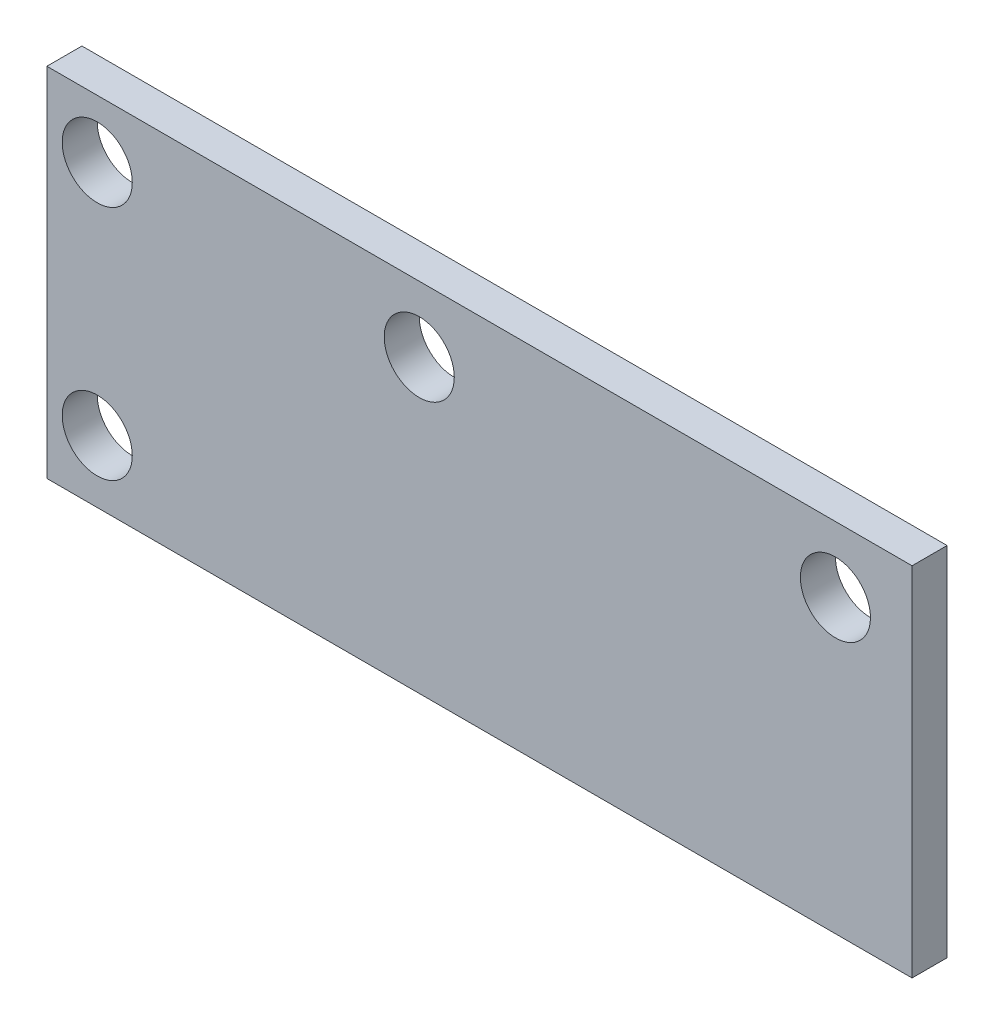
SolidWorks part; units mm, degrees
ref_plane "Piano frontale" through (0, 0, 0) normal (0, 0, 1) x (1, 0, 0)
ref_plane "Piano superiore" through (0, 0, 0) normal (0, 1, 0) x (1, 0, 0)
ref_plane "Piano destro" through (0, 0, 0) normal (1, 0, 0) x (0, 0, -1)
sketch "Schizzo1" plane through (0, 0, 0) normal (0, 0, 1) x (1, 0, 0)
  line L1 (-19.75, -8.15) -> (19.75, -8.15)
  line L2 (-19.75, -8.15) -> (-19.75, 8.15)
  line L3 (-19.75, 8.15) -> (19.75, 8.15)
  line L4 (19.75, -8.15) -> (19.75, 8.15)
  line L5 (-19.75, -8.15) -> (19.75, 8.15) construction
  line L6 (-19.75, 8.15) -> (19.75, -8.15) construction
  point P0 (0, 0)
  dimension "D1" = 16.3
  dimension "D2" = 39.5
extrude "Estrusione-Estrusione1" add sketch "Schizzo1" along normal blind 1.6
sketch "Schizzo2" plane through (0, 0, 1.6) normal (0, 0, 1) x (1, 0, 0)
  line L0 (19.75, 8.15) -> (-19.75, 8.15) construction
  line L1 (19.75, -8.15) -> (19.75, 8.15) construction
  line L2 (-19.75, 8.15) -> (-19.75, -8.15) construction
  circle A0 centre (-2.75, 5.15) radius 1.6
  circle A1 centre (16.25, 5.15) radius 1.6
  circle A2 centre (-17.4515, 5.5) radius 1.6
  circle A3 centre (-17.4515, -5.3) radius 1.6
  dimension "D1" = 19
  dimension "D2" = 3.2
  dimension "D3" = 3
  dimension "D6" = 2.2985
  dimension "D7" = 2.65
  dimension "D4" = 3.5
  dimension "D5" = 10.8
extrude "Taglio-Estrusione1" cut sketch "Schizzo2" against normal through all
